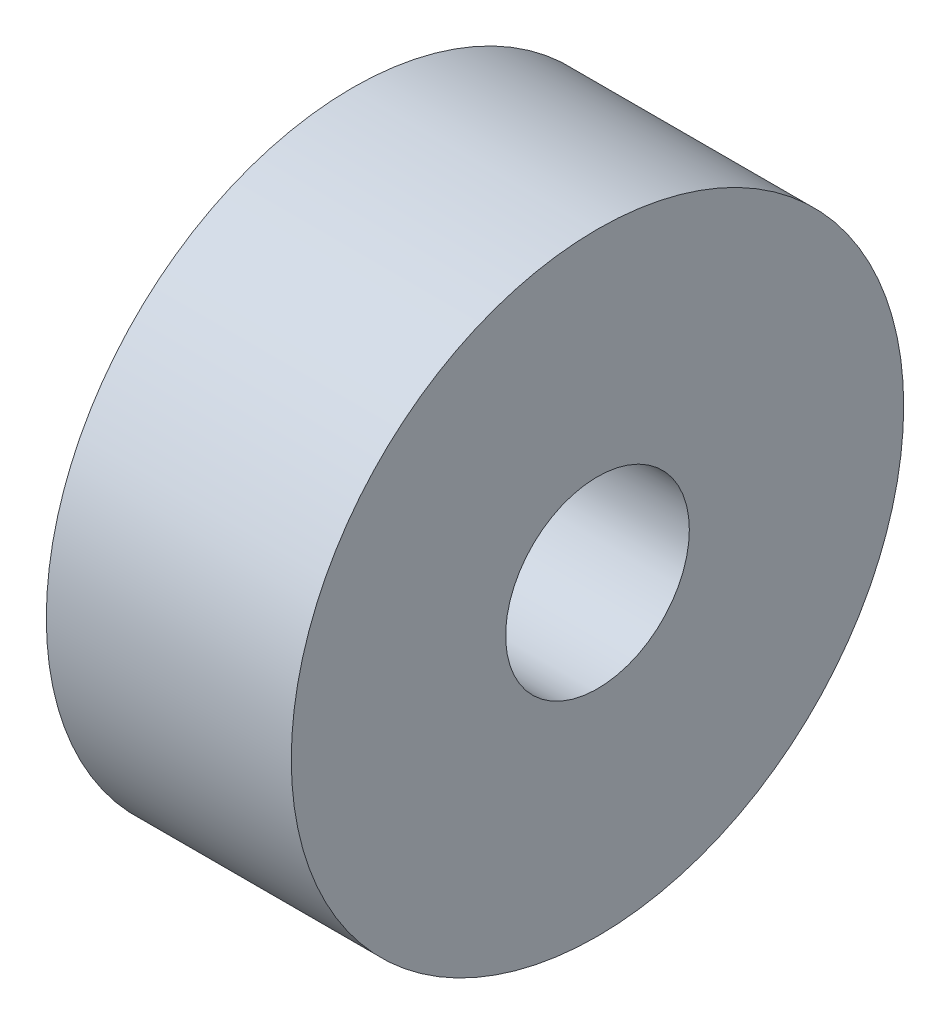
SolidWorks part; units mm, degrees
ref_plane "Plan de face" through (0, 0, 0) normal (0, 0, 1) x (1, 0, 0)
ref_plane "Plan de dessus" through (0, 0, 0) normal (0, 1, 0) x (1, 0, 0)
ref_plane "Plan de droite" through (0, 0, 0) normal (1, 0, 0) x (0, 0, -1)
sketch "Esquisse2" plane through (0, 0, 0) normal (0, 0, 1) x (1, 0, 0)
  line L0 (-2.5081, 0) -> (7.408, 0) construction
  line L1 (0, 0) -> (4, 0)
  line L2 (0, 0) -> (0, 5)
  line L3 (0, 5) -> (4, 5)
  line L4 (4, 0) -> (4, 5)
  dimension "D1" = 4
  dimension "D2" = 5
revolve "Révolution2" add sketch "Esquisse2" angle 360 about L0
sketch "Esquisse3" plane through (0, 0, 0) normal (1, 0, 0) x (0, 0, -1)
  circle A0 centre (0, 0) radius 1.5
  dimension "D1" = 3
extrude "Enlèv. mat.-Extru.4" cut sketch "Esquisse3" along normal through all
